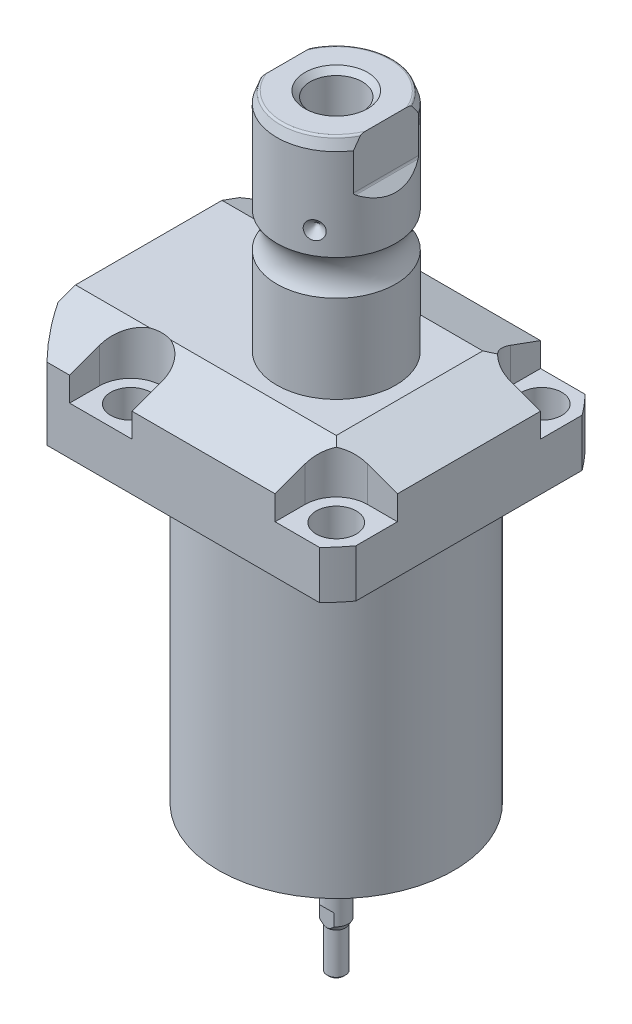
SolidWorks part; units mm, degrees
material "Alloy Steel"
ref_plane "Front Plane" through (0, 0, 0) normal (0, 0, 1) x (1, 0, 0)
ref_plane "Top Plane" through (0, 0, 0) normal (0, 1, 0) x (1, 0, 0)
ref_plane "Right Plane" through (0, 0, 0) normal (1, 0, 0) x (0, 0, -1)
sketch "Sketch1" plane through (0, 0, 0) normal (0, -1, 0) x (0, 0, 1)
  line L0 (-35.433, 50.063) -> (35.433, 50.063)
  line L1 (35.433, 50.063) -> (35.433, -35.433)
  line L2 (35.433, -35.433) -> (-35.433, -35.433)
  line L3 (-35.433, -35.433) -> (-35.433, 50.063)
  line L4 (0, 0) -> (0, -60.6467) construction
  dimension "D1" = 35.433
  dimension "D2" = 85.496
  dimension "D3" = 70.866
extrude "Extrude1" add sketch "Sketch1" against normal blind 104.4448
sketch "Sketch2" plane through (0, 0, 0) normal (0, -1, 0) x (1, 0, 0)
  circle A0 centre (-5.4102, 0) radius 50.8
  dimension "D1" = 101.6
  dimension "D2" = 5.4102
extrude "Cut-Extrude1" cut sketch "Sketch2" against normal through all flip side to cut
sketch "Sketch3" plane through (0, 0, 0) normal (1, 0, 0) x (0, 0, -1)
  line L0 (31.3945, 0) -> (31.3945, 79.4258)
  line L1 (31.3945, 79.4258) -> (76.5937, 79.4258)
  line L2 (76.5937, 79.4258) -> (76.5937, 0)
  line L3 (76.5937, 0) -> (31.3945, 0)
  line L4 (0, -93.345) -> (0, 4.445) construction
  line L5 (24.2233, 0) -> (-24.2233, 0) construction
  dimension "D1" = 62.789
  dimension "D2" = 153.1874
  dimension "D3" = 79.4258
revolve "Cut-Revolve1" cut sketch "Sketch3" angle 360 about L4
fillet "Fillet1" radius 0.381 1 edges at (0, 79.4258, -31.3945)
sketch "Sketch4" plane through (0, 104.4448, 0) normal (0, 1, 0) x (-1, 0, 0)
  line L0 (-35.433, -30.2072) -> (-35.433, 30.2072) construction
  line L1 (41.8127, 35.433) -> (-30.9923, 35.433) construction
  line L2 (-19.1008, -35.433) -> (-19.1008, -27.432)
  line L3 (-35.433, -35.433) -> (-19.1008, -35.433)
  line L4 (-35.433, -19.1008) -> (-35.433, -35.433)
  line L5 (-27.432, -19.1008) -> (-35.433, -19.1008)
  line L6 (35.7632, -35.433) -> (19.1008, -35.433)
  line L7 (19.1008, 35.433) -> (19.1008, 27.432)
  line L8 (35.7632, 35.433) -> (35.7632, 27.432)
  line L9 (35.7632, 35.433) -> (19.1008, 35.433)
  line L10 (-27.432, 19.1008) -> (-35.433, 19.1008)
  line L11 (-35.433, 19.1008) -> (-35.433, 35.433)
  line L12 (-35.433, 35.433) -> (-19.1008, 35.433)
  line L13 (-19.1008, 35.433) -> (-19.1008, 27.432)
  line L14 (-48.9217, 0) -> (49.4551, 0) construction
  line L15 (35.7632, -35.433) -> (35.7632, -27.432)
  line L16 (19.1008, -35.433) -> (19.1008, -27.432)
  arc A0 (19.1008, -27.432) -> (35.7632, -27.432) centre (27.432, -27.432) cw
  arc A1 (-27.432, -19.1008) -> (-19.1008, -27.432) centre (-27.432, -27.432) cw
  arc A2 (-27.432, 19.1008) -> (-19.1008, 27.432) centre (-27.432, 27.432) ccw
  arc A3 (19.1008, 27.432) -> (35.7632, 27.432) centre (27.432, 27.432) ccw
  dimension "D2" = 8.3312
  dimension "D1" = 27.432
  dimension "D3" = 27.432
  dimension "D4" = 54.864
extrude "Cut-Extrude2" cut sketch "Sketch4" against normal blind 12.243
sketch "Sketch5" plane through (0, 0, 0) normal (1, 0, 0) x (0, 0, -1)
  line L0 (-19.558, 104.4448) -> (-35.433, 98.6668)
  line L1 (0, 0) -> (0, 154.1081) construction
  line L2 (-19.558, 104.4448) -> (-35.433, 104.4448)
  line L3 (-35.433, 104.4448) -> (-35.433, 98.6668)
  dimension "D1" = 15.875
  dimension "D2" = 20
extrude "Cut-Extrude9" cut sketch "Sketch5" against normal through all and the other way through all
mirror "Mirror1" about plane through (0, 0, 0) normal (0, 0, 1) of "Cut-Extrude9"
sketch "Sketch9" plane through (0, 0, 0) normal (0, 0, 1) x (1, 0, 0)
  line L0 (19.558, 104.4448) -> (35.433, 98.6668)
  line L1 (35.433, 98.6668) -> (35.433, 104.4448)
  line L2 (35.433, 104.4448) -> (19.558, 104.4448)
  dimension "D1" = 15.875
  dimension "D2" = 20
extrude "Cut-Extrude7" cut sketch "Sketch9" against normal through all and the other way through all
ref_plane "Plane14" through (-35.0774, 0, 0) normal (1, 0, 0) x (0, 0, -1)
sketch "Sketch20" plane through (-35.0774, 88.9, -18.1102) normal (1, 0, 0) x (0, 1, 0)
  line L0 (-88.9, 18.1102) -> (39.8401, 18.1102) construction
  line L1 (-7.2797, 32.639) -> (36.9042, 32.639) construction
  line L2 (-9.4742, 38.3413) -> (-8.0264, 38.3413)
  line L3 (-9.4742, -6.1131) -> (-9.4742, 42.3335) construction
  line L4 (-8.0264, 38.3413) -> (-8.0264, 35.8902)
  line L5 (-8.0264, 35.8902) -> (-7.0104, 35.8902)
  line L6 (-7.0104, 35.8902) -> (-7.0104, 33.8836)
  line L7 (-7.0104, 33.8836) -> (3.9624, 33.8836)
  line L8 (3.9624, 33.8836) -> (3.9624, 32.639)
  line L9 (3.9624, 32.639) -> (-9.4742, 32.639)
  line L10 (-9.4742, 38.3413) -> (-9.4742, 32.639)
  dimension "D1" = 14.5288
  dimension "D2" = 11.4046
  dimension "D3" = 1.4478
  dimension "D4" = 6.5024
  dimension "D5" = 1.016
  dimension "D6" = 2.4892
  dimension "D7" = 10.9728
revolve "Cut-Revolve4" cut sketch "Sketch20" angle 360 about L1
mirror "Mirror10" about plane through (0, 0, 0) normal (0, 0, 1) of "Cut-Revolve4"
sketch "Sketch10" plane through (-35.0774, 88.9, -18.1102) normal (1, 0, 0) x (0, 1, 0)
  line L0 (-1.0325, 3.5814) -> (1.5659, 3.5814) construction
  line L1 (3.9624, 4.826) -> (-7.0104, 4.826) construction
  line L2 (-7.0104, 2.3368) -> (3.9624, 2.3368) construction
  line L4 (-9.4742, -12.097) -> (-9.4742, 48.3174) construction
  circle A0 centre (-9.2075, 8.1026) radius 1.1811
  dimension "D1" = 2.3622
  dimension "D2" = 0.2667
  dimension "D3" = 9.0424
revolve "Revolve4" add sketch "Sketch10" angle 360 about L0
mirror "Mirror12" about plane through (0, 0, 0) normal (0, 0, 1) of bodies 135
sketch "Sketch15" plane through (0, 0, 0) normal (1, 0, 0) x (0, 0, -1)
  line L0 (0, 104.4448) -> (15.875, 104.4448)
  line L1 (15.875, 104.4448) -> (15.875, 127.8297)
  line L2 (15.875, 137.2439) -> (15.875, 161.7218)
  line L3 (14.8118, 164.6428) -> (0, 164.6428)
  line L4 (0, 164.6428) -> (0, 104.4448)
  line L5 (0, 250.2908) -> (0, 28.9095) construction
  line L6 (19.558, 104.4448) -> (-19.558, 104.4448) construction
  line L7 (14.8118, 164.6428) -> (15.875, 161.7218)
  line L9 (24.2233, 79.4258) -> (35.433, 79.4258) construction
  arc A0 (15.875, 137.2439) -> (15.875, 127.8297) centre (22.2504, 132.5368) ccw
  dimension "D2" = 20
  dimension "D4" = 7.9248
  dimension "D6" = 28.6512
  dimension "D1" = 85.217
  dimension "D3" = 31.75
  dimension "D5" = 32.106
  dimension "D7" = 2.921
revolve "Revolve3" add sketch "Sketch15" angle 360 about L5
hole_wizard "Hole1" positions "Sketch18" profile "Sketch17" legacy end condition up to next
sketch "Sketch18" plane through (0, 92.2018, 0) normal (0, 1, 0) x (-1, 0, 0)
  arc A0 (35.7632, -27.432) -> (19.1008, -27.432) centre (27.432, -27.432) ccw construction
  arc A1 (19.1008, 27.432) -> (35.7632, 27.432) centre (27.432, 27.432) ccw construction
  arc A2 (-27.432, 19.1008) -> (-19.1008, 27.432) centre (-27.432, 27.432) ccw construction
  arc A3 (-19.1008, -27.432) -> (-27.432, -19.1008) centre (-27.432, -27.432) ccw construction
  point P0 (-27.432, -27.432)
  point P1 (-27.432, 27.432)
  point P3 (27.432, 27.432)
  point P5 (27.432, -27.432)
sketch "Sketch17" plane through (27.432, 92.2018, -27.432) normal (1, 0, 0) x (0, 0, 1)
  line L0 (0, 0) -> (0, 12.776)
  line L1 (0, 12.776) -> (5.3594, 12.776)
  line L2 (5.3594, 12.776) -> (5.3594, 0)
  line L3 (5.3594, 0) -> (0, 0)
  line L4 (0, 110) -> (0, -10) construction
  dimension "Diameter" = 10.7188
  dimension "Depth" = 12.776
chamfer "Chamfer1" distance 0.635 angle 45 2 edges at (-35.0774, 81.8896, 13.2842) (-35.0774, 81.8896, -13.2842)
ref_plane "Plane15" through (0, 91.9226, 0) normal (0, -1, 0) x (1, 0, 0)
sketch "Sketch21" plane through (0, 91.9226, 0) normal (0, -1, 0) x (1, 0, 0)
  line L0 (-57.5495, -12.9794) -> (-2.9353, -12.9794) construction
  line L1 (-50.063, -1.9304) -> (-49.809, -1.9304)
  line L2 (-49.809, -1.9304) -> (-49.809, -6.7564)
  line L3 (-49.809, -6.7564) -> (-47.2563, -7.4404)
  line L4 (-46.6957, -8.001) -> (-30.759, -8.001)
  line L5 (-30.759, -8.001) -> (-30.759, -12.9794)
  line L6 (-30.759, -12.9794) -> (-50.063, -12.9794)
  line L7 (-50.063, 24.2233) -> (-50.063, -24.2233) construction
  line L8 (-50.063, -12.9794) -> (-50.063, -1.9304)
  line L9 (-47.2563, -7.4404) -> (-46.6957, -8.001)
  dimension "D1" = 12.9794
  dimension "D2" = 0.254
  dimension "D3" = 22.098
  dimension "D4" = 45
  dimension "D5" = 2.5527
  dimension "D6" = 9.9568
  dimension "D7" = 19.05
  dimension "D8" = 15
  dimension "D9" = 12.446
revolve "Cut-Revolve5" cut sketch "Sketch21" angle 360 about L0
mirror "Mirror13" about plane through (0, 0, 0) normal (0, 0, 1) of "Cut-Revolve5"
fillet "Fillet2" radius 0.635 1 edges at (0, 164.6428, 14.8118)
sketch "Sketch26" plane through (0, 0, 0) normal (0, 0, 1) x (1, 0, 0)
  line L0 (-39.772, 143.2048) -> (35.3173, 143.2048) construction
  line L1 (-15.875, 145.6178) -> (-13.462, 143.2048)
  line L2 (-15.875, 161.7218) -> (-15.875, 137.2439) construction
  line L3 (-13.462, 143.2048) -> (-15.875, 143.2048)
  line L4 (-15.875, 143.2048) -> (-15.875, 145.6178)
  arc A0 (-15.875, 127.8297) -> (-15.875, 137.2439) centre (-22.2504, 132.5368) ccw construction
  dimension "D1" = 45
  dimension "D2" = 4.826
  dimension "D3" = 10.668
revolve "Cut-Revolve7" cut sketch "Sketch26" angle 360 about L0
pattern_circular "CirPattern1" count 3 over 360 about axis through (0, 250.2908, 0) along (0, 1, 0) of "Cut-Revolve7"
hole_wizard "Hole2" positions "Sketch28" profile "Sketch27" legacy
sketch "Sketch28" plane through (0, 164.6428, 0) normal (0, 1, 0) x (-1, 0, 0)
  circle A0 centre (0, 0) radius 15.875 construction
  point P0 (0, 0)
sketch "Sketch27" plane through (0, 164.6428, 0) normal (1, 0, 0) x (0, 0, 1)
  line L0 (0, 0) -> (0, 28.8121)
  line L1 (0, 28.8121) -> (6.9469, 24.638)
  line L2 (6.9469, 24.638) -> (6.9469, 0)
  line L4 (6.9469, 0) -> (0, 0)
  line L6 (0, 28.8121) -> (-6.9469, 24.638) construction
  line L7 (0, -4.2442) -> (0, 117.3081) construction
  dimension "Diameter" = 13.8938
  dimension "Depth" = 24.638
  dimension "Drill Angle" = 118
sketch "Sketch29" plane through (0, 0, 0) normal (0, 0, 1) x (1, 0, 0)
  line L0 (0, 0) -> (0, 192.0172) construction
  line L1 (13.284, 164.6428) -> (13.284, 151.9428)
  line L2 (14.3672, 164.6428) -> (-14.3672, 164.6428) construction
  line L3 (13.5072, 151.404) -> (16.332, 148.5792)
  line L5 (16.332, 148.5792) -> (16.332, 164.6428)
  line L6 (16.332, 164.6428) -> (13.284, 164.6428)
  line L7 (-16.332, 164.6428) -> (-13.284, 164.6428)
  line L8 (-16.332, 148.5792) -> (-16.332, 164.6428)
  line L9 (-13.5072, 151.404) -> (-16.332, 148.5792)
  line L10 (-13.284, 164.6428) -> (-13.284, 151.9428)
  arc A0 (13.284, 151.9428) -> (13.5072, 151.404) centre (14.046, 151.9428) ccw
  arc A1 (-13.284, 151.9428) -> (-13.5072, 151.404) centre (-14.046, 151.9428) cw
  dimension "D2" = 0.762
  dimension "D1" = 45
  dimension "D3" = 26.568
  dimension "D4" = 12.7
  dimension "D5" = 3.048
extrude "Cut-Extrude10" cut sketch "Sketch29" against normal through all and the other way through all
chamfer "Chamfer2" distance 1.4351 angle 45 1 edges at (0, 164.6428, 6.9469)
sketch "Sketch30" plane through (0, 0, 0) normal (0, -1, 0) x (1, 0, 0)
  line L0 (0, 0) -> (18.7689, -5.0291) construction
  line L2 (47.0228, 0) -> (-47.0228, 0) construction
  line L3 (0, 0) -> (-9.7155, -16.8277) construction
  line L4 (0, 0) -> (-13.7398, -13.7398) construction
  line L5 (0, 0) -> (-9.7155, 16.8277) construction
  line L7 (0, 0) -> (-5.0291, 18.7689) construction
  circle A0 centre (0, 0) radius 19.431 construction
  circle A1 centre (19.431, 0) radius 1.27
  circle A2 centre (18.7689, -5.0291) radius 1.27
  circle A3 centre (-9.7155, -16.8277) radius 1.27
  circle A4 centre (-13.7398, -13.7398) radius 1.27
  circle A5 centre (-9.7155, 16.8277) radius 1.27
  circle A6 centre (-5.0291, 18.7689) radius 1.27
  dimension "D1" = 38.862
  dimension "D7" = 2.54
  dimension "D8" = 2.54
  dimension "D9" = 2.54
  dimension "D10" = 2.54
  dimension "D11" = 2.54
  dimension "D12" = 2.54
  dimension "D2" = 15
  dimension "D3" = 120
  dimension "D4" = 15
  dimension "D5" = 120
  dimension "D6" = 15
extrude "Cut-Extrude11" cut sketch "Sketch30" against normal blind 7.62
sketch "Sketch31" plane through (0, 0, 0) normal (1, 0, 0) x (0, 0, -1)
  line L0 (0, 61.6176) -> (0, -19.4362) construction
  line L2 (14.351, 0) -> (14.351, 1.3208)
  line L3 (-31.3945, 0) -> (31.3945, 0) construction
  line L4 (14.351, 1.3208) -> (11.6459, 1.3208)
  line L5 (11.6459, 1.3208) -> (11.6459, 0)
  line L6 (11.6459, 0) -> (14.351, 0)
  dimension "D1" = 1.3208
  dimension "D2" = 28.702
  dimension "D3" = 23.2918
revolve "Cut-Revolve8" cut sketch "Sketch31" angle 360 about L0
sketch "Sketch32" plane through (0, 0, 0) normal (1, 0, 0) x (0, 0, -1)
  line L0 (0, 46.6429) -> (0, -27.2479) construction
  line L2 (3.175, 0) -> (3.175, -26.4864)
  line L3 (-31.3945, 0) -> (31.3945, 0) construction
  line L4 (3.175, -26.4864) -> (2.4384, -27.7622)
  line L5 (2.4384, -27.7622) -> (2.4384, -38.6842)
  line L6 (2.4384, -38.6842) -> (1.9304, -39.1922)
  line L7 (1.9304, -39.1922) -> (0, -39.1922)
  line L8 (0, -39.1922) -> (0, 0)
  line L9 (0, 0) -> (3.175, 0)
  line L10 (-5.4728, 164.6428) -> (-14.3672, 164.6428) construction
  dimension "D1" = 6.35
  dimension "D2" = 4.8768
  dimension "D3" = 30
  dimension "D4" = 11.43
  dimension "D5" = 45
  dimension "D6" = 0.508
  dimension "D7" = 203.835
revolve "Revolve5" add sketch "Sketch32" angle 360 about L0
sketch "Sketch33" plane through (0, 0, 0) normal (1, 0, 0) x (0, 0, -1)
  line L0 (2.5019, -27.6522) -> (2.5019, -23.3172)
  line L4 (2.4384, -27.7622) -> (3.175, -26.4864) construction
  line L7 (2.5019, -23.3172) -> (3.2639, -22.5552)
  line L12 (3.2639, -22.5552) -> (3.2639, -27.6522)
  line L13 (2.5019, -27.6522) -> (3.2639, -27.6522)
  line L14 (0, 47.0228) -> (0, -47.0228) construction
  line L15 (-1.9304, -39.1922) -> (1.9304, -39.1922) construction
  dimension "D1" = 2.5019
  dimension "D2" = 45
  dimension "D3" = 0.762
  dimension "D4" = 15.875
extrude "Cut-Extrude12" cut sketch "Sketch33" against normal mid plane 6.35
mirror "Mirror14" about plane through (0, 0, 0) normal (0, 0, 1) of "Cut-Extrude12"
